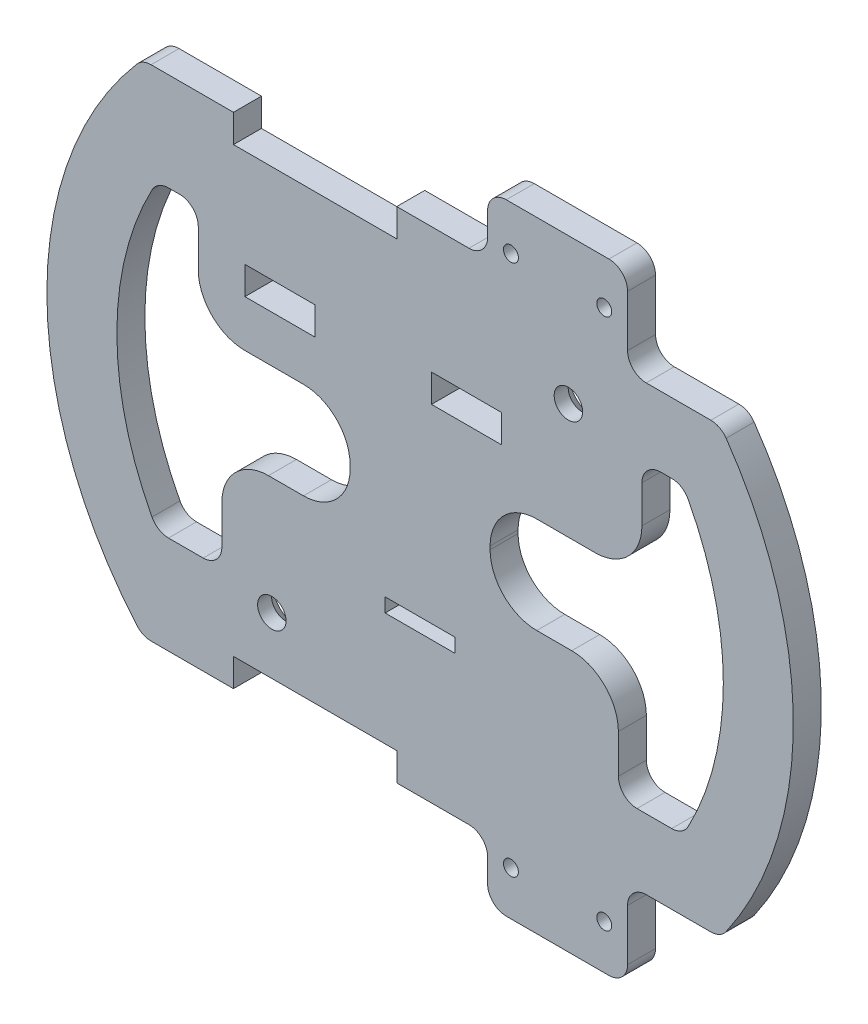
SolidWorks part; units mm, degrees
material "Acrílico (médio-alto impacto)"
ref_plane "Plano frontal" through (0, 0, 0) normal (0, 0, 1) x (1, 0, 0)
ref_plane "Plano superior" through (0, 0, 0) normal (0, 1, 0) x (1, 0, 0)
ref_plane "Plano direito" through (0, 0, 0) normal (1, 0, 0) x (0, 0, -1)
sketch "Esboço1" plane through (0, 0, 0) normal (0, 0, 1) x (1, 0, 0)
  line L0 (80, 0) -> (0, 0) construction
  line L1 (-80, -66.5) -> (80, -66.5)
  line L2 (-80, -66.5) -> (-80, 66.5)
  line L3 (-80, 66.5) -> (80, 66.5)
  line L4 (80, -66.5) -> (80, 66.5)
  line L5 (-80, -66.5) -> (80, 66.5) construction
  line L6 (-80, 66.5) -> (80, -66.5) construction
  line L7 (80, 47.5) -> (-80, 47.5) construction
  line L8 (80, -47.5) -> (-80, -47.5) construction
  line L9 (14.4719, 66.5) -> (14.4719, 53.5)
  line L10 (0, 0) -> (0, 66.5) construction
  line L11 (44.4719, 47.5) -> (44.4719, 66.5)
  line L12 (44.4719, -47.5) -> (44.4719, -66.5)
  line L13 (14.4719, -66.5) -> (14.4719, -53.5)
  line L14 (14.4719, 53.5) -> (-59.479, 53.5)
  line L15 (14.4719, -53.5) -> (-59.479, -53.5)
  line L16 (-5.0035, 47.5) -> (-40.0035, 47.5)
  line L17 (-5.0035, 47.5) -> (-5.0035, 53.5)
  line L18 (-31.7837, -35.2994) -> (31.7837, 35.2994) construction
  line L19 (-42.5, -20.2) -> (-42.5, -14.2) construction
  line L20 (-7.5, -20.2) -> (7.5, -20.2)
  line L21 (-7.5, -20.2) -> (-7.5, -23.2)
  line L22 (-7.5, -23.2) -> (7.5, -23.2)
  line L23 (7.5, -20.2) -> (7.5, -23.2)
  line L24 (-7.5, -20.2) -> (7.5, -23.2) construction
  line L25 (-7.5, -23.2) -> (7.5, -20.2) construction
  line L26 (-37.55, 26.5) -> (-22.55, 26.5)
  line L27 (-37.55, 26.5) -> (-37.55, 20.5)
  line L28 (-37.55, 20.5) -> (-22.55, 20.5)
  line L29 (-22.55, 26.5) -> (-22.55, 20.5)
  line L30 (-37.55, 26.5) -> (-22.55, 20.5) construction
  line L31 (-37.55, 20.5) -> (-22.55, 26.5) construction
  line L32 (17.45, 20.5) -> (2.45, 20.5)
  line L33 (17.45, 20.5) -> (17.45, 26.5)
  line L34 (17.45, 26.5) -> (2.45, 26.5)
  line L35 (2.45, 20.5) -> (2.45, 26.5)
  line L36 (17.45, 20.5) -> (2.45, 26.5) construction
  line L37 (17.45, 26.5) -> (2.45, 20.5) construction
  line L38 (-42.5, -14.2) -> (42.5, -14.2) construction
  line L39 (42.5, -14.2) -> (42.5, -20.2) construction
  line L40 (42.5, -20.2) -> (-42.5, -20.2) construction
  line L41 (-56.2917, 32.5) -> (-47.55, 32.5)
  line L42 (-47.55, 32.5) -> (-47.55, 10.5)
  line L43 (-47.55, 10.5) -> (-15, 10.5)
  line L44 (-15, 10.5) -> (-15, -10.2)
  line L47 (-42.5, -32.5) -> (-56.2917, -32.5)
  line L48 (-42.5, -32.5) -> (-42.5, -10.2)
  line L49 (-42.5, -10.2) -> (-15, -10.2)
  line L50 (15, -10.2) -> (15, 10.5)
  line L51 (15, 10.5) -> (47.55, 10.5)
  line L52 (47.55, 10.5) -> (47.55, 32.5)
  line L53 (47.55, 32.5) -> (56.2917, 32.5)
  line L54 (56.2917, -32.5) -> (42.5, -32.5)
  line L55 (15, -10.2) -> (42.5, -10.2)
  line L56 (42.5, -10.2) -> (42.5, -32.5)
  line L57 (15, 10.5) -> (-15, 10.5) construction
  line L58 (-21.0674, -35.2994) -> (-42.5, -35.2994) construction
  line L59 (-5.0035, 53.5) -> (-40.0035, 53.5)
  line L60 (-40.0035, 47.5) -> (-40.0035, 53.5)
  line L61 (-5.0035, 47.5) -> (-40.0035, 53.5) construction
  line L62 (-5.0035, 53.5) -> (-40.0035, 47.5) construction
  line L63 (-5.0035, -53.5) -> (-40.0035, -53.5)
  line L64 (-40.0035, -47.5) -> (-40.0035, -53.5)
  line L65 (-5.0035, -47.5) -> (-40.0035, -47.5)
  line L66 (-5.0035, -47.5) -> (-5.0035, -53.5)
  line L67 (24.9009, 47.5) -> (24.9009, 66.5) construction
  line L69 (44.4719, 47.5) -> (64.372, 47.5)
  line L70 (44.4719, -47.5) -> (64.372, -47.5)
  line L73 (-56.2917, 32.5) -> (-56.2917, 53.5)
  line L74 (-56.2917, -32.5) -> (-56.2917, -56.8441)
  line L75 (56.2917, 32.5) -> (56.2917, 47.5)
  line L76 (56.2917, -32.5) -> (56.2917, -56.8441)
  circle A0 centre (0, 0) radius 80
  circle A1 centre (-31.7837, -35.2994) radius 3.05
  circle A2 centre (31.7837, 35.2994) radius 3.05
  circle A3 centre (19.4719, 57) radius 1.6
  circle A8 centre (19.4719, -57) radius 1.6
  arc A9 (-56.2917, -32.5) -> (-56.2917, 32.5) centre (0, 0) cw
  arc A10 (56.2917, -32.5) -> (56.2917, 32.5) centre (0, 0) ccw
  circle A11 centre (39.4719, 57) radius 1.6
  circle A12 centre (39.4719, -57) radius 1.6
  point P0 (0, 0)
  point P17 (-22.5035, 50.5)
  point P22 (44.4719, 66.5)
  point P34 (-30.05, 23.5)
  point P44 (0, -21.7)
  point P53 (9.95, 23.5)
  point P58 (0, -20.2)
  point P65 (-65, 0)
  point P80 (0, 10.5)
  point P83 (24.9009, 57)
  point P84 (-22.5035, 53.5)
  dimension "D6" = 6.1
  dimension "D7" = 6
  dimension "D18" = 15
  dimension "D25" = 3.2
  dimension "D1" = 95
  dimension "D2" = 19
  dimension "D3" = 160
  dimension "D4" = 95
  dimension "D5" = 48
  dimension "D8" = 5
  dimension "D9" = 3
  dimension "D10" = 6
  dimension "D11" = 15
  dimension "D12" = 20.2
  dimension "D13" = 40.7
  dimension "D14" = 25
  dimension "D15" = 2.45
  dimension "D16" = 85
  dimension "D17" = 35
  dimension "D19" = 10
  dimension "D20" = 10
  dimension "D21" = 10
  dimension "D22" = 30
  dimension "D23" = 30
  dimension "D24" = 5
  dimension "D26" = 15
extrude "Ressalto-extrusão1" add sketch "Esboço1" along normal blind 6 contours L74 A9 L73 L14 A0 L15 | L76 L54 L56 L55 L50 L51 L52 L53 L75 L69 L11 L3 L9 L14 L17 L16 L60 L73 L41 L42 L43 L44 L49 L48 L47 L74 L15 L64 L65 L66 L13 L1 L12 L70 A8 A3 A2 A1 L20 L23 L22 L21 L26 | A10 L76 L70 A0 L69 L75
chamfer "Chanfro1" distance 3 angle 45 2 edges at (34.8337, 35.2994, 0) (-28.7337, -35.2994, 0)
fillet "Filete1" radius 4 20 edges at (56.2917, 32.5, 3) (47.55, 32.5, 3) (42.5, -32.5, 3) (56.2917, -32.5, 3) (-42.5, -32.5, 3) (-56.2917, -32.5, 3) (-47.55, 32.5, 3) (-56.2917, 32.5, 3) (14.4719, -53.5, 3) (14.4719, 53.5, 3) (44.4719, 47.5, 3) (44.4719, -47.5, 3) (14.4719, 66.5, 3) (44.4719, 66.5, 3) (44.4719, -66.5, 3) (14.4719, -66.5, 3) (-59.479, 53.5, 3) (64.372, 47.5, 3) (64.372, -47.5, 3) (-59.479, -53.5, 3)
fillet "Filete2" radius 10 4 edges at (15, -10.2, 3) (-15, -10.2, 3) (-15, 10.5, 3) (15, 10.5, 3)
fillet "Filete3" radius 10 4 edges at (47.55, 10.5, 3) (-47.55, 10.5, 3) (42.5, -10.2, 3) (-42.5, -10.2, 3)
